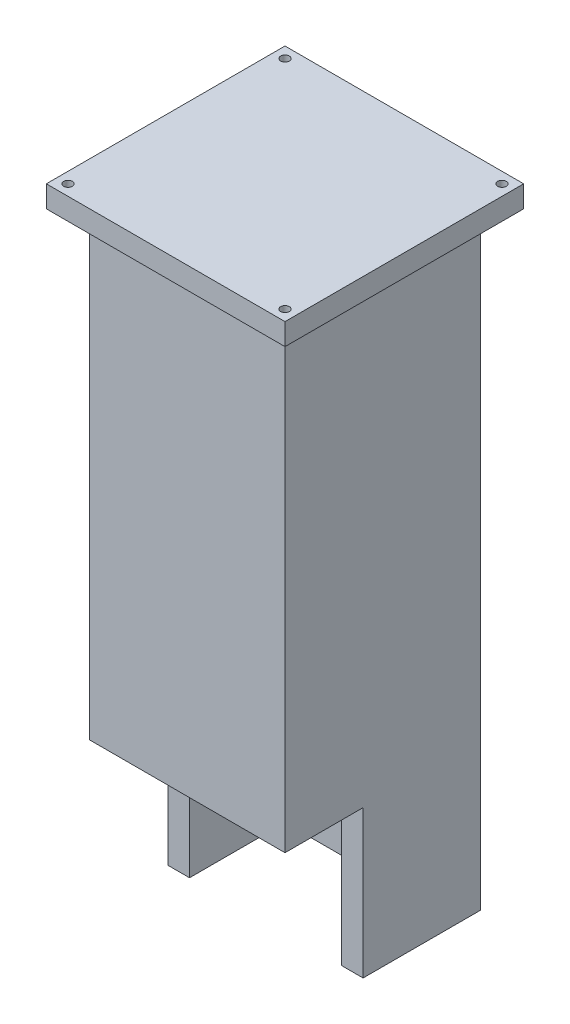
SolidWorks part; units mm, degrees
ref_plane "Alzado" through (0, 0, 0) normal (0, 0, 1) x (1, 0, 0)
ref_plane "Planta" through (0, 0, 0) normal (0, 1, 0) x (1, 0, 0)
ref_plane "Vista lateral" through (0, 0, 0) normal (1, 0, 0) x (0, 0, -1)
sketch "Croquis1" plane through (0, 0, 0) normal (0, 1, 0) x (1, 0, 0)
  line L1 (-22.5, -22.5) -> (22.5, -22.5)
  line L2 (-22.5, -22.5) -> (-22.5, 22.5)
  line L3 (-22.5, 22.5) -> (22.5, 22.5)
  line L4 (22.5, -22.5) -> (22.5, 22.5)
  line L5 (-22.5, -22.5) -> (22.5, 22.5) construction
  line L6 (-22.5, 22.5) -> (22.5, -22.5) construction
  point P0 (0, 0)
  dimension "D1" = 45
  dimension "D2" = 45
extrude "Saliente-Extruir1" add sketch "Croquis1" along normal blind 300
sketch "Croquis4" plane through (-22.5, 0, 0) normal (-1, 0, 0) x (0, 0, 1)
  line L1 (22.5, 300) -> (22.5, 0) construction
  line L3 (55, 0) -> (-55, 0) construction
  line L5 (4.5, 0) -> (4.5, 34)
  line L6 (4.5, 34) -> (22.5, 34)
  line L8 (22.5, 34) -> (22.5, 0)
  line L9 (22.5, 0) -> (4.5, 0)
  dimension "D4" = 34
extrude "Cortar-Extruir2" cut sketch "Croquis4" against normal through all
sketch "Croquis7" plane through (0, 0, 22.5) normal (0, 0, 1) x (1, 0, 0)
  line L0 (0, -24.75) -> (0, 24.75) construction
  line L1 (-22.5, 246.3879) -> (22.5, 246.3879)
  line L2 (-22.5, 246.3879) -> (-22.5, 273.6121)
  line L3 (-22.5, 273.6121) -> (22.5, 273.6121)
  line L4 (22.5, 246.3879) -> (22.5, 273.6121)
  line L5 (-22.5, 246.3879) -> (22.5, 273.6121) construction
  line L6 (-22.5, 273.6121) -> (22.5, 246.3879) construction
  line L7 (22.5, 300) -> (22.5, 34) construction
  point P0 (0, 260)
  dimension "D1" = 260
sketch "Croquis8" plane through (0, 300, 0) normal (0, 1, 0) x (1, 0, 0)
  line L0 (22.5, -22.5) -> (22.5, 22.5) construction
  line L1 (-17.5, -17.5) -> (17.5, -17.5)
  line L2 (-17.5, -17.5) -> (-17.5, 17.5)
  line L3 (-17.5, 17.5) -> (17.5, 17.5)
  line L4 (17.5, -17.5) -> (17.5, 17.5)
  line L5 (-17.5, -17.5) -> (17.5, 17.5) construction
  line L6 (-17.5, 17.5) -> (17.5, -17.5) construction
  line L7 (22.5, 22.5) -> (-22.5, 22.5) construction
  point P0 (0, 0)
  dimension "D1" = 5
  dimension "D2" = 5
extrude "Cortar-Extruir3" cut sketch "Croquis8" against normal through all contours L3 L4 L1 L2
sketch "Croquis9" plane through (0, 0, -22.5) normal (0, 0, -1) x (-1, 0, 0)
  line L0 (22.5, 273.6121) -> (-22.5, 246.3879) construction
  line L1 (-17.5, 249.4128) -> (17.5, 249.4128)
  line L2 (-17.5, 249.4128) -> (-17.5, 270.5872)
  line L3 (-17.5, 270.5872) -> (17.5, 270.5872)
  line L4 (17.5, 249.4128) -> (17.5, 270.5872)
  line L5 (-17.5, 249.4128) -> (17.5, 270.5872) construction
  line L6 (-17.5, 270.5872) -> (17.5, 249.4128) construction
  line L7 (22.5, 246.3879) -> (22.5, 273.6121) construction
  point P0 (0, 260)
  point P10 (22.5, 260)
  dimension "D1" = 5
extrude "Cortar-Extruir4" cut sketch "Croquis9" against normal blind 10 contours L4 L3 L2 L1
sketch "Croquis10" plane through (0, 0, 22.5) normal (0, 0, 1) x (1, 0, 0)
  circle A0 centre (0, 260) radius 1
  dimension "D1" = 2
extrude "Cortar-Extruir5" cut sketch "Croquis10" against normal blind 10
sketch "Croquis11" plane through (0, 0, 22.5) normal (0, 0, 1) x (1, 0, 0)
  line L0 (22.5, 300) -> (22.5, 34) construction
  line L1 (-22.5, 300) -> (22.5, 300)
  line L2 (-22.5, 300) -> (-22.5, 273.6121)
  line L3 (-22.5, 273.6121) -> (22.5, 273.6121)
  line L4 (22.5, 300) -> (22.5, 273.6121)
  line L5 (-22.5, 273.6121) -> (22.5, 273.6121) construction
  dimension "D1" = 0
extrude "Cortar-Extruir6" cut sketch "Croquis11" against normal through all
sketch "Croquis12" plane through (0, 0, 22.5) normal (0, 0, 1) x (1, 0, 0)
  line L0 (-22.5, 267.3717) -> (22.5, 246.3879)
  line L1 (-22.5, 246.3879) -> (-22.5, 273.6121) construction
  line L2 (-22.5, 246.3879) -> (22.5, 246.3879) construction
  dimension "D1" = 25
sketch "Croquis13" plane through (0, 0, 0) normal (1, 0, 0) x (0, 0, -1)
  line L0 (-22.5, 273.6121) -> (-22.5, 34) construction
  line L1 (-22.5, 140) -> (22.5, 140)
  line L10 (-22.5, 140) -> (-22.5, 273.6121)
  line L11 (-22.5, 273.6121) -> (22.5, 273.6121)
  line L12 (22.5, 140) -> (22.5, 273.6121)
  dimension "D1" = 133.6121
extrude "Cortar-Extruir9" cut sketch "Croquis13" against normal through all both and the other way through all
sketch "Croquis14" plane through (0, 140, 0) normal (0, 1, 0) x (1, 0, 0)
  line L1 (-27.5, -27.5) -> (27.5, -27.5)
  line L2 (-27.5, -27.5) -> (-27.5, 27.5)
  line L3 (-27.5, 27.5) -> (27.5, 27.5)
  line L4 (27.5, -27.5) -> (27.5, 27.5)
  line L5 (-27.5, -27.5) -> (27.5, 27.5) construction
  line L6 (-27.5, 27.5) -> (27.5, -27.5) construction
  circle A0 centre (-25, 25) radius 1
  circle A1 centre (25, -25) radius 1
  circle A2 centre (25, 25) radius 1
  circle A3 centre (-25, -25) radius 1
  point P0 (0, 0)
  dimension "D7" = 2
  dimension "D1" = 27.5
  dimension "D2" = 27.5
  dimension "D3" = 2.5
  dimension "D4" = 2.5
  dimension "D5" = 2.5
  dimension "D6" = 2.5
extrude "Saliente-Extruir3" add sketch "Croquis14" along normal blind 5
